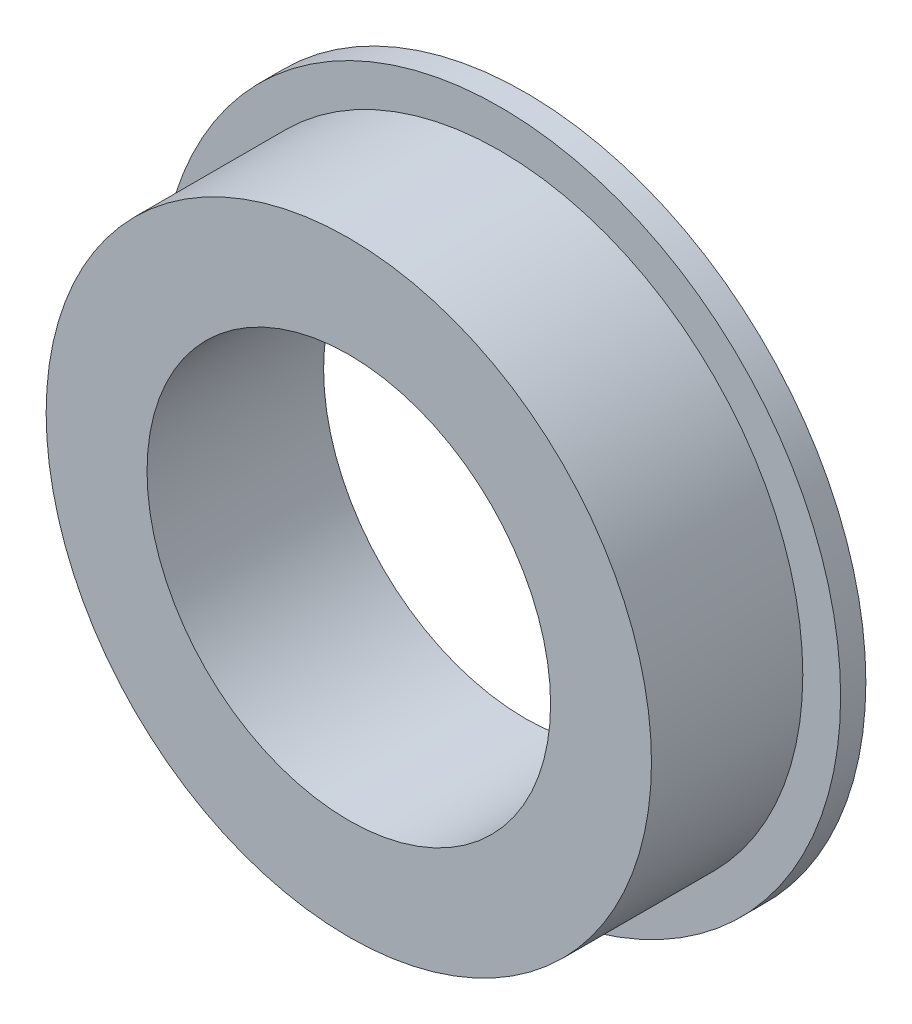
SolidWorks part; units mm, degrees
ref_plane "前视基准面" through (0, 0, 0) normal (0, 0, 1) x (1, 0, 0)
ref_plane "上视基准面" through (0, 0, 0) normal (0, 1, 0) x (1, 0, 0)
ref_plane "右视基准面" through (0, 0, 0) normal (1, 0, 0) x (0, 0, -1)
sketch "Sketch1" plane through (0, 0, 0) normal (0, 0, 1) x (1, 0, 0)
  circle A0 centre (0, 0) radius 6.75
  circle A1 centre (0, 0) radius 4
  dimension "D1" = 13.5
  dimension "D2" = 8
extrude "Boss-Extrude1" add sketch "Sketch1" along normal blind 0.5
sketch "Sketch2" plane through (0, 0, 0.5) normal (0, 0, 1) x (1, 0, 0)
  circle A0 centre (0, 0) radius 6
  circle A1 centre (0, 0) radius 4 construction
  circle A2 centre (0, 0) radius 4
  dimension "D1" = 2
extrude "Boss-Extrude2" add sketch "Sketch2" along normal blind 3
